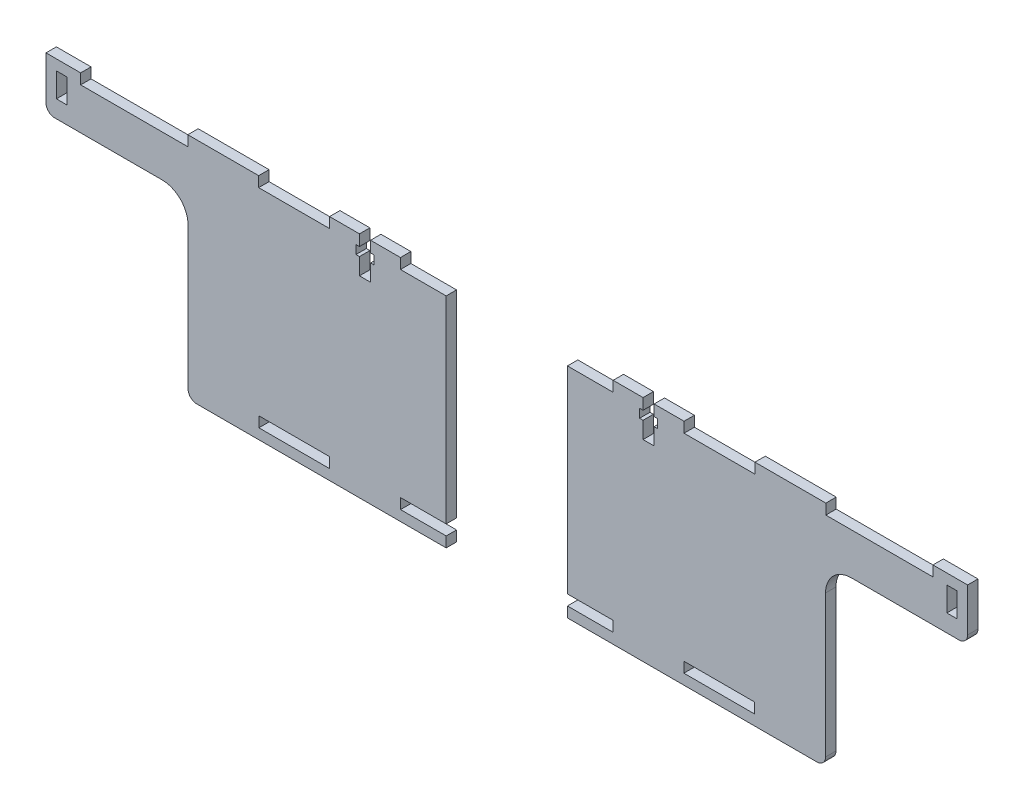
SolidWorks part; units mm, degrees
ref_plane "Front Plane" through (0, 0, 0) normal (0, 0, 1) x (1, 0, 0)
ref_plane "Top Plane" through (0, 0, 0) normal (0, 1, 0) x (1, 0, 0)
ref_plane "Right Plane" through (0, 0, 0) normal (1, 0, 0) x (0, 0, -1)
sketch "Sketch2" plane through (0, 0, 0) normal (0, 0, 1) x (1, 0, 0)
  line L0 (-133, 33) -> (133, 33)
  line L1 (133, 33) -> (133, 18)
  line L2 (133, 18) -> (92, 18)
  line L3 (92, 18) -> (92, -33)
  line L4 (92, -33) -> (-92, -33)
  line L5 (-92, -33) -> (-92, 18)
  line L6 (-92, 18) -> (-133, 18)
  line L7 (-133, 18) -> (-133, 33)
  point P2 (0, 33)
  dimension "D1" = 184
  dimension "D2" = 266
  dimension "D3" = 15
  dimension "D4" = 66
  dimension "D5" = 33
extrude "Boss-Extrude1" add sketch "Sketch2" along normal blind 3
sketch "Sketch3" plane through (0, 0, 3) normal (0, 0, 1) x (1, 0, 0)
  line L0 (130, 25.5) -> (133, 25.5) construction
  line L1 (-130, 23) -> (-127, 23)
  line L2 (-130, 23) -> (-130, 30)
  line L3 (-130, 30) -> (-127, 30)
  line L4 (-127, 23) -> (-127, 30)
  line L5 (-130, 23) -> (-127, 30) construction
  line L6 (-130, 30) -> (-127, 23) construction
  line L7 (127, 23) -> (130, 23)
  line L8 (127, 23) -> (127, 30)
  line L9 (127, 30) -> (130, 30)
  line L10 (130, 23) -> (130, 30)
  line L11 (127, 23) -> (130, 30) construction
  line L12 (127, 30) -> (130, 23) construction
  line L13 (133, 18) -> (133, 33) construction
  line L14 (-130, 26.5) -> (-133, 26.5) construction
  line L15 (-133, 33) -> (-133, 18) construction
  line L16 (-130, 30) -> (-130, 33) construction
  line L17 (133, 33) -> (-133, 33) construction
  line L18 (92, 18) -> (133, 18) construction
  line L20 (-92, -30) -> (-71.5556, -30) construction
  line L21 (-71.5556, -30) -> (-51.1111, -30)
  line L22 (-71.5556, -30) -> (-71.5556, -27)
  line L23 (-71.5556, -27) -> (-51.1111, -27)
  line L24 (-51.1111, -30) -> (-51.1111, -27)
  line L25 (-71.5556, -30) -> (-51.1111, -27) construction
  line L26 (-71.5556, -27) -> (-51.1111, -30) construction
  line L27 (-30.6667, -30) -> (-10.2222, -30)
  line L28 (-30.6667, -30) -> (-30.6667, -27)
  line L29 (-30.6667, -27) -> (-10.2222, -27)
  line L30 (-10.2222, -30) -> (-10.2222, -27)
  line L31 (-30.6667, -30) -> (-10.2222, -27) construction
  line L32 (-30.6667, -27) -> (-10.2222, -30) construction
  line L33 (10.2222, -30) -> (30.6667, -30)
  line L34 (10.2222, -30) -> (10.2222, -27)
  line L35 (10.2222, -27) -> (30.6667, -27)
  line L36 (30.6667, -30) -> (30.6667, -27)
  line L37 (10.2222, -30) -> (30.6667, -27) construction
  line L38 (10.2222, -27) -> (30.6667, -30) construction
  line L39 (51.1111, -30) -> (71.5556, -30)
  line L40 (51.1111, -30) -> (51.1111, -27)
  line L41 (51.1111, -27) -> (71.5556, -27)
  line L42 (71.5556, -30) -> (71.5556, -27)
  line L43 (51.1111, -30) -> (71.5556, -27) construction
  line L44 (51.1111, -27) -> (71.5556, -30) construction
  line L45 (-92, 18) -> (-92, -33) construction
  line L46 (-51.1111, -30) -> (-30.6667, -30) construction
  line L47 (-10.2222, -30) -> (10.2222, -30) construction
  line L48 (30.6667, -30) -> (51.1111, -30) construction
  line L49 (71.5556, -30) -> (92, -30) construction
  line L50 (92, -33) -> (92, 18) construction
  line L51 (-92, -33) -> (92, -33) construction
  line L52 (-133, 30) -> (-112.5385, 30) construction
  line L53 (-112.5385, 30) -> (-92.0769, 30)
  line L54 (-112.5385, 30) -> (-112.5385, 33)
  line L55 (-112.5385, 33) -> (-92.0769, 33)
  line L56 (-92.0769, 30) -> (-92.0769, 33)
  line L57 (-112.5385, 30) -> (-92.0769, 33) construction
  line L58 (-112.5385, 33) -> (-92.0769, 30) construction
  line L59 (-71.6154, 30) -> (-51.1538, 30)
  line L60 (-71.6154, 30) -> (-71.6154, 33)
  line L61 (-71.6154, 33) -> (-51.1538, 33)
  line L62 (-51.1538, 30) -> (-51.1538, 33)
  line L63 (-71.6154, 30) -> (-51.1538, 33) construction
  line L64 (-71.6154, 33) -> (-51.1538, 30) construction
  line L65 (-30.6923, 30) -> (-10.2308, 30)
  line L66 (-30.6923, 30) -> (-30.6923, 33)
  line L67 (-30.6923, 33) -> (-10.2308, 33)
  line L68 (-10.2308, 30) -> (-10.2308, 33)
  line L69 (-30.6923, 30) -> (-10.2308, 33) construction
  line L70 (-30.6923, 33) -> (-10.2308, 30) construction
  line L71 (10.2308, 30) -> (30.6923, 30)
  line L72 (10.2308, 30) -> (10.2308, 33)
  line L73 (10.2308, 33) -> (30.6923, 33)
  line L74 (30.6923, 30) -> (30.6923, 33)
  line L75 (10.2308, 30) -> (30.6923, 33) construction
  line L76 (10.2308, 33) -> (30.6923, 30) construction
  line L77 (51.1538, 30) -> (71.6154, 30)
  line L78 (51.1538, 30) -> (51.1538, 33)
  line L79 (51.1538, 33) -> (71.6154, 33)
  line L80 (71.6154, 30) -> (71.6154, 33)
  line L81 (51.1538, 30) -> (71.6154, 33) construction
  line L82 (51.1538, 33) -> (71.6154, 30) construction
  line L83 (92.0769, 30) -> (112.5385, 30)
  line L84 (92.0769, 30) -> (92.0769, 33)
  line L85 (92.0769, 33) -> (112.5385, 33)
  line L86 (112.5385, 30) -> (112.5385, 33)
  line L87 (92.0769, 30) -> (112.5385, 33) construction
  line L88 (92.0769, 33) -> (112.5385, 30) construction
  line L89 (-92.0769, 30) -> (-71.6154, 30) construction
  line L90 (-51.1538, 30) -> (-30.6923, 30) construction
  line L91 (-10.2308, 30) -> (10.2308, 30) construction
  line L92 (30.6923, 30) -> (51.1538, 30) construction
  line L93 (71.6154, 30) -> (92.0769, 30) construction
  line L94 (112.5385, 30) -> (133, 30) construction
  line L95 (-123, 30) -> (-112.5385, 30)
  line L96 (-123, 30) -> (-123, 33)
  line L97 (-123, 33) -> (-112.5385, 33)
  line L98 (-112.5385, 30) -> (-112.5385, 33)
  line L99 (-123, 30) -> (-112.5385, 33) construction
  line L100 (-123, 33) -> (-112.5385, 30) construction
  line L101 (123, 30) -> (112.5385, 30)
  line L102 (123, 30) -> (123, 33)
  line L103 (123, 33) -> (112.5385, 33)
  line L104 (112.5385, 30) -> (112.5385, 33)
  line L105 (123, 30) -> (112.5385, 33) construction
  line L106 (123, 33) -> (112.5385, 30) construction
  point P0 (-128.5, 26.5)
  point P5 (128.5, 26.5)
  point P18 (117.7692, 31.5)
  point P24 (-61.3333, -28.5)
  point P29 (-20.4444, -28.5)
  point P34 (20.4444, -28.5)
  point P39 (61.3333, -28.5)
  point P45 (-61.3846, 31.5)
  point P55 (-20.4615, 31.5)
  point P62 (-102.3077, 31.5)
  point P67 (20.4615, 31.5)
  point P72 (61.3846, 31.5)
  point P77 (102.3077, 31.5)
  point P103 (-117.7692, 31.5)
  line M16 (133, 33) -> (-133, 33)
  dimension "D1" = 3
  dimension "D2" = 3
  dimension "D3" = 3
  dimension "D4" = 3
  dimension "D5" = 5
  dimension "D6" = 4
extrude "Cut-Extrude1" cut sketch "Sketch3" against normal through all both and the other way through all contours L1 L4 L3 L2 | L96 L95 L54 M16 | L53 L56 L54 M16 | L59 L62 L60 M16 | L65 L68 L66 M16 | L71 L74 L72 M16 | L77 L80 L78 M16 | L83 L86 L84 M16 | L101 L102 L86 M16 | L7 L10 L9 L8 | L21 L24 L23 L22 | L27 L30 L29 L28 | L33 L36 L35 L34 | L39 L42 L41 L40
fillet "Fillet1" radius 7.5 2 edges at (-92, 18, 1.5) (92, 18, 1.5)
fillet "Fillet2" radius 2.5 4 edges at (-92, -33, 1.5) (92, -33, 1.5) (133, 18, 1.5) (-133, 18, 1.5)
sketch "Sketch4" plane through (0, 0, 3) normal (0, 0, 1) x (1, 0, 0)
  line L0 (-30.6923, 33) -> (-51.1538, 33) construction
  line L1 (-42.5231, 22.5) -> (-39.3231, 22.5)
  line L2 (-42.5231, 22.5) -> (-42.5231, 33)
  line L3 (-42.5231, 33) -> (-39.3231, 33)
  line L4 (-39.3231, 22.5) -> (-39.3231, 33)
  line L5 (-42.5231, 22.5) -> (-39.3231, 33) construction
  line L6 (-42.5231, 33) -> (-39.3231, 22.5) construction
  line L7 (51.1538, 33) -> (30.6923, 33) construction
  line L8 (39.3231, 22.5) -> (42.5231, 22.5)
  line L9 (39.3231, 22.5) -> (39.3231, 33)
  line L10 (39.3231, 33) -> (42.5231, 33)
  line L11 (42.5231, 22.5) -> (42.5231, 33)
  line L12 (39.3231, 22.5) -> (42.5231, 33) construction
  line L13 (39.3231, 33) -> (42.5231, 22.5) construction
  line L14 (40.9231, 33) -> (40.9231, 29.825) construction
  line L15 (38.3231, 29.825) -> (43.5231, 29.825)
  line L16 (38.3231, 29.825) -> (38.3231, 27.325)
  line L17 (38.3231, 27.325) -> (43.5231, 27.325)
  line L18 (43.5231, 29.825) -> (43.5231, 27.325)
  line L19 (38.3231, 29.825) -> (43.5231, 27.325) construction
  line L20 (38.3231, 27.325) -> (43.5231, 29.825) construction
  line L21 (-43.5231, 29.825) -> (-38.3231, 29.825)
  line L22 (-43.5231, 29.825) -> (-43.5231, 27.325)
  line L23 (-43.5231, 27.325) -> (-38.3231, 27.325)
  line L24 (-38.3231, 29.825) -> (-38.3231, 27.325)
  line L25 (-43.5231, 29.825) -> (-38.3231, 27.325) construction
  line L26 (-43.5231, 27.325) -> (-38.3231, 29.825) construction
  line L27 (-40.9231, 33) -> (-40.9231, 29.825) construction
  point P0 (-40.9231, 27.75)
  point P7 (40.9231, 27.75)
  point P14 (40.9231, 28.575)
  point P19 (-40.9231, 28.575)
  point P24 (-40.9231, 33)
  point P26 (40.9231, 33)
  dimension "D1" = 2.5
  dimension "D2" = 5.2
  dimension "D3" = 3.2
  dimension "D4" = 10.5
  dimension "D5" = 3.175
extrude "Cut-Extrude2" cut sketch "Sketch4" against normal through all both and the other way through all contours L8 L11 L10 L9 | L16 L17 L18 L15 | L1 L4 L3 L2 | L24 L23 L22 L21
sketch "Sketch5" plane through (0, 0, 3) normal (0, 0, 1) x (1, 0, 0)
  line L0 (10.2308, 33) -> (-10.2308, 33) construction
  line L1 (-17.5, -33) -> (17.5, -33)
  line L2 (-17.5, -33) -> (-17.5, 33)
  line L3 (-17.5, 33) -> (17.5, 33)
  line L4 (17.5, -33) -> (17.5, 33)
  line L5 (-17.5, -33) -> (17.5, 33) construction
  line L6 (-17.5, 33) -> (17.5, -33) construction
  line L7 (-89.5, -33) -> (89.5, -33) construction
  point P0 (0, 0)
  point P9 (0, 0)
  point P10 (0, 0)
  point P11 (-21.133, 0)
  dimension "D1" = 35
extrude "Cut-Extrude3" cut sketch "Sketch5" against normal through all both and the other way through all
